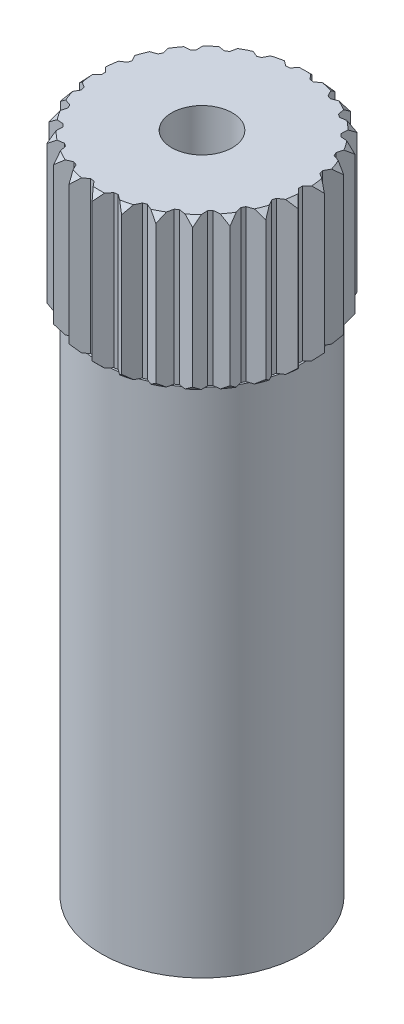
SolidWorks part; units mm, degrees
material "Brass"
ref_plane "Front Plane" through (0, 0, 0) normal (0, 0, 1) x (1, 0, 0)
ref_plane "Top Plane" through (0, 0, 0) normal (0, 1, 0) x (1, 0, 0)
ref_plane "Right Plane" through (0, 0, 0) normal (1, 0, 0) x (0, 0, -1)
sketch "ShaftS" plane through (0, 0, 0) normal (0, 1, 0) x (1, 0, 0)
  circle A0 centre (0, 0) radius 2.9
  dimension "Dia" = 5.8
extrude "SHAFT" add sketch "ShaftS" along normal blind 13.5
sketch "ShaftExtensionS" plane through (0, 13.5, 0) normal (0, 1, 0) x (1, 0, 0)
  circle A0 centre (0, 0) radius 2.6
  circle A1 centre (0, 0) radius 2.9 construction
  dimension "DiaControl" = 0.3
extrude "SHAFT EXTENSION" add sketch "ShaftExtensionS" along normal blind 4
sketch "ToothS" plane through (0, 17.5, 0) normal (0, 1, 0) x (1, 0, 0)
  line L0 (0, 2.6) -> (0, 2.9) construction
  line L1 (0, 2.9) -> (-0.2629, 2.5867)
  line L2 (0, 2.9) -> (0.2629, 2.5867)
  line L3 (-0.2629, 2.5867) -> (0.2629, 2.5867) construction
  arc A0 (0.2629, 2.5867) -> (-0.2629, 2.5867) centre (0, 0) ccw
  circle A3 centre (0, 0) radius 2.6 construction
  circle A4 centre (0, 0) radius 2.9 construction
  dimension "D1" = 80
  dimension "D2" = 0.5258
  dimension "D3" = 0.3
extrude "TOOTH" add sketch "ToothS" against normal up to body (17.5 mm away) separate body
pattern_circular "TOOTH CP" count 26 over 360 about axis through (0, 0, 0) along (0, 1, 0) of "TOOTH"
sketch "SmallBoreS" plane through (0, 17.5, 0) normal (0, 1, 0) x (1, 0, 0)
  circle A0 centre (0, 0) radius 0.8
  dimension "Dia" = 1.6
extrude "SMALL BORE" cut sketch "SmallBoreS" against normal blind 4
sketch "ShaftUnderCutS" plane through (0, 0, 0) normal (0, 0, 1) x (1, 0, 0)
  line L0 (2.9, 0) -> (2.65, 0)
  line L1 (2.65, 0) -> (2.65, 13.5)
  line L2 (2.65, 13.5) -> (2.9, 13.5)
  line L3 (2.9, 13.5) -> (2.9, 0)
  line L4 (0, 0) -> (2.65, 0) construction
  line L5 (2.7115, 13.5) -> (2.3867, 13.5) construction
  line L6 (0, 13.5) -> (0, 0) construction
  dimension "DiaControl" = 0.25
  dimension "RefDiaInner" = 2.65
  dimension "RefDiaOuter" = 2.9
revolve "SHAFT UNDER CUT" cut sketch "ShaftUnderCutS" angle 360 about axis through (0, 13.5, 0) along (0, -1, 0)
sketch "TeethChamferS" plane through (0, 0, 0) normal (1, 0, 0) x (0, 0, -1)
  line L0 (2.9, 17.3232) -> (2.9, 17.5)
  line L1 (2.9, 17.5) -> (2.7232, 17.5)
  line L2 (2.7232, 17.5) -> (2.9, 17.3232)
  line L3 (2.9, 13.5) -> (2.9, 17.5) construction
  line L4 (2.9, 15.5) -> (0, 15.5) construction
  line L5 (0, 17.5) -> (0, 13.5) construction
  line L6 (2.7232, 13.5) -> (2.9, 13.6768)
  line L7 (2.9, 13.5) -> (2.7232, 13.5)
  line L8 (2.9, 13.6768) -> (2.9, 13.5)
  point P4 (2.9, 15.5)
  dimension "D1" = 45
  dimension "Length" = 0.25
revolve "TEETH CHAMFER" cut sketch "TeethChamferS" angle 360 about axis through (0, 13.5, 0) along (0, 1, 0)
